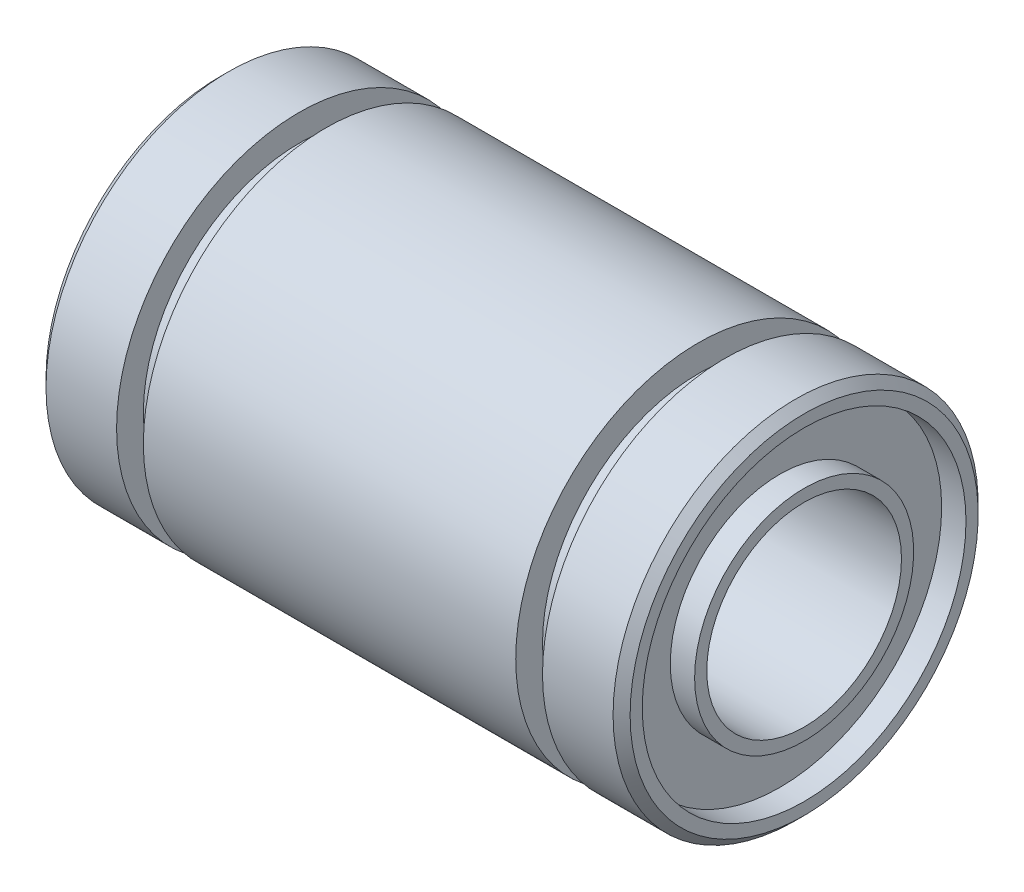
SolidWorks part; units mm, degrees
material "1060 Alloy"
ref_plane "Front Plane" through (0, 0, 0) normal (0, 0, 1) x (1, 0, 0)
ref_plane "Top Plane" through (0, 0, 0) normal (0, 1, 0) x (1, 0, 0)
ref_plane "Right Plane" through (0, 0, 0) normal (1, 0, 0) x (0, 0, -1)
sketch "Sketch1" plane through (0, 0, 0) normal (0, 0, 1) x (1, 0, 0)
  line L0 (-45.6895, 0) -> (45.6895, 0) construction
  line L1 (-11.65, 7.5) -> (-8.75, 7.5)
  line L2 (-8.75, 7.5) -> (-8.75, 6.4)
  line L3 (-8.75, 6.4) -> (-7.65, 6.4)
  line L4 (-7.65, 6.4) -> (-7.65, 7.5)
  line L5 (-7.65, 7.5) -> (7.65, 7.5)
  line L6 (0, 45.6895) -> (0, -45.6895) construction
  line L7 (-11.65, 7.5) -> (-12, 7.15)
  line L8 (-12, 7.15) -> (-12, 6.65)
  line L9 (-12, 6.65) -> (-11, 6.65)
  line L10 (-11, 6.65) -> (-11, 4.5)
  line L11 (-11, 4.5) -> (-12, 4.5)
  line L12 (-12, 4.5) -> (-12, 4)
  line L13 (-12, 4) -> (12, 4)
  line L14 (12, 4.5) -> (12, 4)
  line L15 (11, 4.5) -> (12, 4.5)
  line L16 (11, 6.65) -> (11, 4.5)
  line L17 (12, 6.65) -> (11, 6.65)
  line L18 (12, 7.15) -> (12, 6.65)
  line L19 (11.65, 7.5) -> (12, 7.15)
  line L20 (7.65, 6.4) -> (7.65, 7.5)
  line L21 (8.75, 6.4) -> (7.65, 6.4)
  line L22 (8.75, 7.5) -> (8.75, 6.4)
  line L23 (11.65, 7.5) -> (8.75, 7.5)
  point P19 (0, 4)
  point P26 (0, 7.5)
  dimension "D1" = 45
  dimension "D2" = 1.1
  dimension "L" = 24
  dimension "B" = 17.5
  dimension "W" = 1.1
  dimension "D" = 7.5
  dimension "D_1" = 7.15
  dimension "D3" = 0.5
  dimension "dr" = 4
  dimension "D4" = 0.5
  dimension "D5" = 1
revolve "Revolve1" add sketch "Sketch1" angle 360 about L0
ref_plane "mate1" through (0, 0, -5) normal (0, 0, 1) x (1, 0, 0)
ref_plane "mate2" through (0, 0, 5) normal (0, 0, 1) x (1, 0, 0)
equation "\"D\"=15"
equation "\"D1\"=14.3"
equation "\"dr\"=8"
equation "\"L\"=24"
equation "\"B\"=17.5"
equation "\"W\"=1.1"
equation "\"L@Sketch1\"= \"L\""
equation "\"B@Sketch1\"= \"B\""
equation "\"W@Sketch1\"= \"W\""
equation "\"dr@Sketch1\"= \"dr\" * 0.5"
equation "\"D@Sketch1\" = \"D\" * 0.5"
equation "\"D_1@Sketch1\" = \"D1\" * 0.5"
